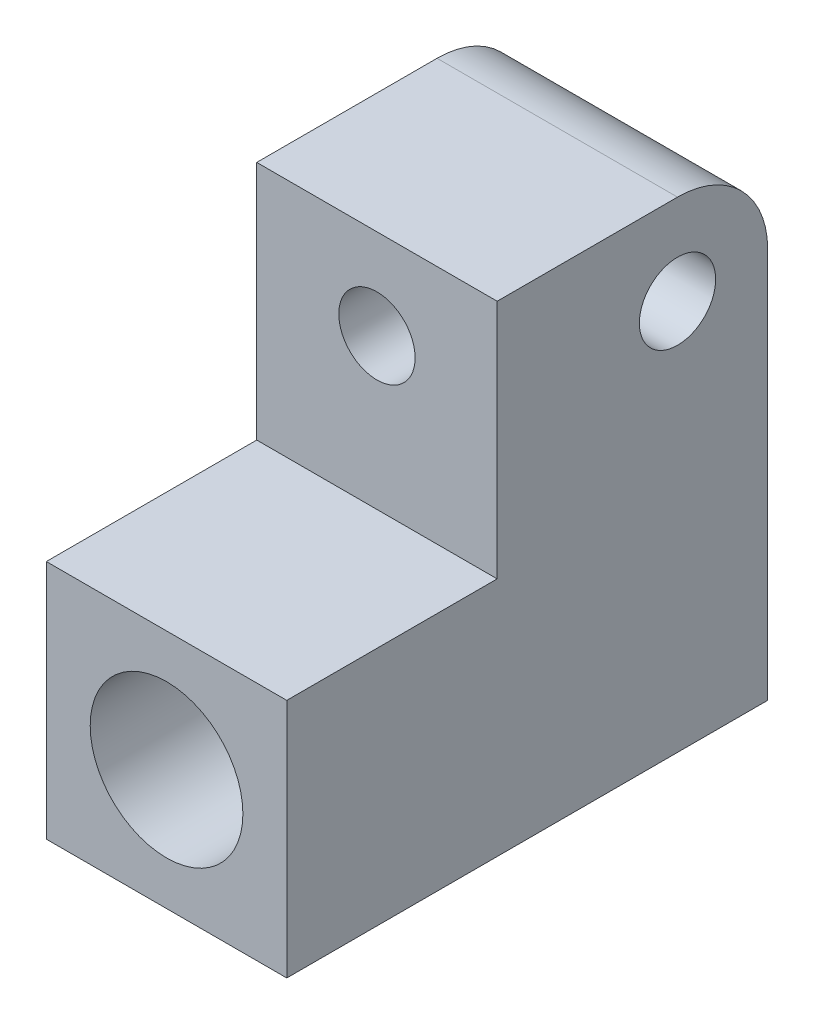
SolidWorks part; units mm, degrees
ref_plane "Front Plane" through (0, 0, 0) normal (0, 0, 1) x (1, 0, 0)
ref_plane "Top Plane" through (0, 0, 0) normal (0, 1, 0) x (1, 0, 0)
ref_plane "Right Plane" through (0, 0, 0) normal (1, 0, 0) x (0, 0, -1)
sketch "Sketch3" plane through (0, 0, 0) normal (0, 1, 0) x (1, 0, 0)
  line L0 (-10, 20) -> (10, -20) construction
  line L1 (-10, 20) -> (10, 20)
  line L2 (-10, 20) -> (-10, -20)
  line L3 (-10, -20) -> (10, -20)
  line L4 (10, 20) -> (10, -20)
  dimension "D1" = 20
  dimension "D2" = 40
extrude "Boss-Extrude2" add sketch "Sketch3" along normal mid plane 40
fillet "Fillet2" radius 7.5 1 edges at (0, 20, -20)
sketch "Sketch4" plane through (-10, 0, 0) normal (-1, 0, 0) x (0, 0, 1)
  circle A0 centre (-12.5, 12.5) radius 3.175
  dimension "D1" = 6.35
extrude "Cut-Extrude2" cut sketch "Sketch4" against normal through all
sketch "Sketch5" plane through (0, 20, 0) normal (0, 1, 0) x (1, 0, 0)
  line L0 (-10, 12.5) -> (-10, -20) construction
  line L1 (-10, -2.5) -> (10, -2.5)
  line L2 (-10, -2.5) -> (-10, -20)
  line L3 (-10, -20) -> (10, -20)
  line L4 (10, -2.5) -> (10, -20)
  line L6 (10, 12.5) -> (-10, 12.5) construction
  dimension "D1" = 15
extrude "Cut-Extrude3" cut sketch "Sketch5" against normal blind 20
sketch "Sketch6" plane through (0, 0, 2.5) normal (0, 0, 1) x (1, 0, 0)
  line L0 (-10, 12.5) -> (10, 12.5) construction
  line L1 (-10, 0) -> (-10, 20) construction
  line L2 (10, 0) -> (10, 20) construction
  circle A0 centre (0, 12.5) radius 3.175
  dimension "D1" = 6.35
extrude "Cut-Extrude4" cut sketch "Sketch6" against normal up to next
sketch "Sketch7" plane through (0, 0, 20) normal (0, 0, 1) x (1, 0, 0)
  line L0 (-10, 0) -> (10, -20) construction
  line L1 (10, 0) -> (10, -20) construction
  circle A0 centre (0, -10) radius 6.35
  dimension "D1" = 12.7
extrude "Cut-Extrude5" cut sketch "Sketch7" against normal through all
